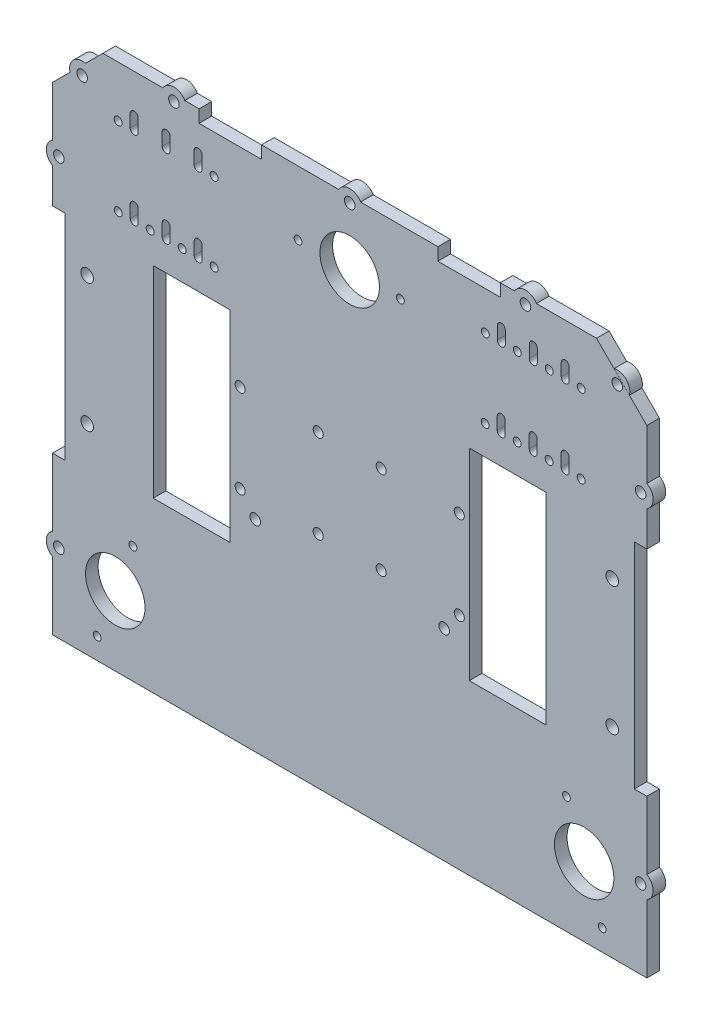
SolidWorks part; units mm, degrees
ref_plane "Front Plane" through (0, 0, 0) normal (0, 0, 1) x (1, 0, 0)
ref_plane "Top Plane" through (0, 0, 0) normal (0, 1, 0) x (1, 0, 0)
ref_plane "Right Plane" through (0, 0, 0) normal (1, 0, 0) x (0, 0, -1)
sketch "Sketch1" plane through (0, 0, 0) normal (0, 0, 1) x (1, 0, 0)
  line L0 (64.2262, -107) -> (118, -107)
  line L1 (-98, 103) -> (98, 103)
  line L3 (-118, -107) -> (-64.2262, -107)
  line L5 (-150, 100) -> (150, -100) construction
  line L6 (-150, -100) -> (150, 100) construction
  line L10 (0, 0) -> (0, 48.5738) construction
  line L12 (-47.5, 0) -> (47.5, 0) construction
  line L13 (47.5, -40) -> (47.5, 40)
  line L14 (47.5, 40) -> (78, 40)
  line L15 (78, 40) -> (78, -40)
  line L16 (78, -40) -> (47.5, -40)
  line L17 (-78, -40) -> (-47.5, -40)
  line L18 (-47.5, -40) -> (-47.5, 40)
  line L19 (-78, 40) -> (-78, -40)
  line L20 (-47.5, 40) -> (-78, 40)
  line L21 (78, 0) -> (118, 0) construction
  line L22 (118, 83) -> (118, -107)
  line L23 (-118, 83) -> (-118, -107)
  line L24 (-98, 103) -> (-98, 83) construction
  line L25 (-98, 83) -> (-118, 83) construction
  line L26 (0, 103) -> (0, -97) construction
  line L27 (-118, 83) -> (-98, 103)
  line L28 (98, 103) -> (118, 83)
  arc A0 (64.2262, -107) -> (-64.2262, -107) centre (0, -97) ccw
  point P0 (0, 0)
  point P19 (0, 0)
  point P22 (47.5, 0)
  point P33 (118, 0)
  dimension "D2" = 130
  dimension "D1" = 210
  dimension "D3" = 63
  dimension "D4" = 20
  dimension "D5" = 20
  dimension "D6" = 95
  dimension "D7" = 80
  dimension "D8" = 30.5
  dimension "D9" = 40
extrude "Boss-Extrude1" add sketch "Sketch1" along normal blind 5
sketch "Sketch2" plane through (0, 0, 5) normal (0, 0, 1) x (1, 0, 0)
  circle A0 centre (43.5, 15.5) radius 2
  circle A1 centre (43.5, -19.5) radius 2
  circle A2 centre (12.5, -19.5) radius 2
  circle A3 centre (12.5, 15.5) radius 2
  circle A4 centre (-12.5, 15.5) radius 2
  circle A5 centre (-12.5, -19.5) radius 2
  circle A6 centre (-43.5, -19.5) radius 2
  circle A7 centre (-43.5, 15.5) radius 2
extrude "Cut-Extrude1" cut sketch "Sketch2" against normal through all
sketch "Sketch3" plane through (0, 0, 5) normal (0, 0, 1) x (1, 0, 0)
  line L0 (-85.5875, 82.747) -> (-85.5875, 87.747) construction
  line L1 (-85.5875, 85.247) -> (-88.4029, 85.247) construction
  line L2 (-84, 87.747) -> (-84, 82.747)
  line L3 (-87.175, 87.747) -> (-87.175, 82.747)
  line L4 (-72.8875, 82.747) -> (-72.8875, 87.747) construction
  line L5 (-60.1875, 82.747) -> (-60.1875, 87.747) construction
  line L6 (-74.4775, 87.747) -> (-74.475, 82.747)
  line L7 (-71.2975, 87.747) -> (-71.3, 82.747)
  line L8 (-61.7775, 87.747) -> (-61.775, 82.747)
  line L9 (-58.5975, 87.747) -> (-58.6, 82.747)
  line L10 (-83.9734, 56.5828) -> (-83.9734, 51.5828)
  line L11 (-87.1484, 56.5828) -> (-87.1484, 51.5828)
  line L12 (-74.4509, 56.5828) -> (-74.4484, 51.5828)
  line L13 (-71.2709, 56.5828) -> (-71.2734, 51.5828)
  line L14 (-61.7509, 56.5828) -> (-61.7484, 51.5828)
  line L15 (-58.5709, 56.5828) -> (-58.5734, 51.5828)
  line L16 (0, 103) -> (0, 110.8506) construction
  line L17 (98, 103) -> (-98, 103) construction
  line L18 (60.1875, 82.747) -> (60.1875, 87.747) construction
  line L19 (72.8875, 82.747) -> (72.8875, 87.747) construction
  line L20 (85.5875, 85.247) -> (88.4029, 85.247) construction
  line L21 (85.5875, 82.747) -> (85.5875, 87.747) construction
  line L22 (58.5709, 56.5828) -> (58.5734, 51.5828)
  line L23 (61.7509, 56.5828) -> (61.7484, 51.5828)
  line L24 (71.2709, 56.5828) -> (71.2734, 51.5828)
  line L25 (74.4509, 56.5828) -> (74.4484, 51.5828)
  line L26 (87.1484, 56.5828) -> (87.1484, 51.5828)
  line L27 (83.9734, 56.5828) -> (83.9734, 51.5828)
  line L28 (58.5975, 87.747) -> (58.6, 82.747)
  line L29 (61.7775, 87.747) -> (61.775, 82.747)
  line L30 (71.2975, 87.747) -> (71.3, 82.747)
  line L31 (74.4775, 87.747) -> (74.475, 82.747)
  line L32 (87.175, 87.747) -> (87.175, 82.747)
  line L33 (84, 87.747) -> (84, 82.747)
  circle A0 centre (20.1383, 77.5) radius 1.55
  circle A1 centre (-20.5035, 77.5) radius 1.55
  circle A2 centre (-53.8375, 82.747) radius 1.5875
  circle A3 centre (-66.5375, 82.747) radius 1.5875
  circle A4 centre (-79.2375, 82.747) radius 1.5875
  circle A5 centre (-91.9375, 82.747) radius 1.5875
  circle A6 centre (0, 77.5) radius 11.8076
  circle A11 centre (-104.25, 23.5) radius 2.5
  circle A12 centre (-104.25, -27.5) radius 2.5
  circle A13 centre (104.25, 23.5) radius 2.5
  circle A14 centre (104.25, -27.5) radius 2.5
  circle A15 centre (86.0568, -60.5122) radius 1.55
  circle A16 centre (100.255, -98.5932) radius 1.55
  circle A17 centre (-86.0568, -60.5122) radius 1.55
  circle A18 centre (-100.255, -98.5932) radius 1.55
  arc A19 (-87.175, 82.747) -> (-84, 82.747) centre (-85.5875, 82.747) ccw
  arc A20 (-87.175, 87.747) -> (-84, 87.747) centre (-85.5875, 87.747) cw
  arc A21 (-74.475, 82.747) -> (-71.3, 82.747) centre (-72.8875, 82.747) ccw
  arc A22 (-61.775, 82.747) -> (-58.6, 82.747) centre (-60.1875, 82.747) ccw
  arc A23 (-71.2975, 87.747) -> (-74.4775, 87.747) centre (-72.8875, 87.747) ccw
  arc A24 (-58.5975, 87.747) -> (-61.7775, 87.747) centre (-60.1875, 87.747) ccw
  arc A25 (-61.775, 82.747) -> (-58.6, 82.747) centre (-60.1875, 82.747) ccw
  arc A27 (-87.1484, 56.5828) -> (-83.9734, 56.5828) centre (-85.5609, 56.5828) cw
  arc A28 (-87.1484, 51.5828) -> (-83.9734, 51.5828) centre (-85.5609, 51.5828) ccw
  arc A29 (-71.2709, 56.5828) -> (-74.4509, 56.5828) centre (-72.8609, 56.5828) ccw
  arc A30 (-74.4484, 51.5828) -> (-71.2734, 51.5828) centre (-72.8609, 51.5828) ccw
  arc A31 (-58.5709, 56.5828) -> (-61.7509, 56.5828) centre (-60.1609, 56.5828) ccw
  arc A32 (-61.7484, 51.5828) -> (-58.5734, 51.5828) centre (-60.1609, 51.5828) ccw
  circle A33 centre (-91.9109, 51.5828) radius 1.5875
  circle A34 centre (-79.2109, 51.5828) radius 1.5875
  circle A35 centre (-66.5109, 51.5828) radius 1.5875
  circle A36 centre (-53.8109, 51.5828) radius 1.5875
  circle A37 centre (53.8109, 51.5828) radius 1.5875
  circle A38 centre (66.5109, 51.5828) radius 1.5875
  circle A39 centre (79.2109, 51.5828) radius 1.5875
  circle A40 centre (91.9109, 51.5828) radius 1.5875
  arc A41 (61.7484, 51.5828) -> (58.5734, 51.5828) centre (60.1609, 51.5828) cw
  arc A42 (58.5709, 56.5828) -> (61.7509, 56.5828) centre (60.1609, 56.5828) cw
  arc A43 (74.4484, 51.5828) -> (71.2734, 51.5828) centre (72.8609, 51.5828) cw
  arc A44 (71.2709, 56.5828) -> (74.4509, 56.5828) centre (72.8609, 56.5828) cw
  arc A45 (87.1484, 51.5828) -> (83.9734, 51.5828) centre (85.5609, 51.5828) cw
  arc A46 (87.1484, 56.5828) -> (83.9734, 56.5828) centre (85.5609, 56.5828) ccw
  arc A47 (61.775, 82.747) -> (58.6, 82.747) centre (60.1875, 82.747) cw
  arc A48 (58.5975, 87.747) -> (61.7775, 87.747) centre (60.1875, 87.747) cw
  arc A49 (71.2975, 87.747) -> (74.4775, 87.747) centre (72.8875, 87.747) cw
  arc A50 (61.775, 82.747) -> (58.6, 82.747) centre (60.1875, 82.747) cw
  arc A51 (74.475, 82.747) -> (71.3, 82.747) centre (72.8875, 82.747) cw
  arc A52 (87.175, 87.747) -> (84, 87.747) centre (85.5875, 87.747) ccw
  arc A53 (87.175, 82.747) -> (84, 82.747) centre (85.5875, 82.747) cw
  circle A54 centre (91.9375, 82.747) radius 1.5875
  circle A55 centre (79.2375, 82.747) radius 1.5875
  circle A56 centre (66.5375, 82.747) radius 1.5875
  circle A57 centre (53.8375, 82.747) radius 1.5875
  circle A58 centre (93.0921, -79.3816) radius 11.8076
  circle A59 centre (-93.0921, -79.3816) radius 11.8076
  dimension "D4" = 3.18
  dimension "D1" = 5
  dimension "D3" = 5
  dimension "D5" = 2
  dimension "D6" = 2
extrude "Cut-Extrude2" cut sketch "Sketch3" against normal through all contours A6 | A0 | A1 | L7 A23 L6 A21 | L9 A24 L8 A22 | A20 L3 A19 L2 | A5 | A33 | L11 A28 L10 A27 | L12 A30 L13 A29 | A34 | L14 A32 L15 A31 | A35 | A36 | A53 L32 A52 L33 | A55 | A51 L31 A49 L30 | A48 L28 A47 L29 | A57 | A56 | A54 | L26 A46 L27 A45 | A40 | A39 | A44 L24 A43 L25 | A38 | A42 L22 A41 L23 | A37 | A13 | A14 | A58 | A15 | A16 | A11 | A12 | A59 | A18 | A17 | A2
sketch "Sketch4" plane through (0, 0, 5) normal (0, 0, 1) x (1, 0, 0)
  line L0 (-118, -2) -> (-113, -2) construction
  line L1 (-118, 83) -> (-118, -107) construction
  line L2 (-113, 40.5) -> (-113, -44.5)
  line L3 (-113, 40.5) -> (-118, 40.5)
  line L4 (-118, 40.5) -> (-118, -44.5)
  line L5 (-118, -44.5) -> (-113, -44.5)
  line L6 (0, 103) -> (0, 94.0884) construction
  line L7 (98, 103) -> (-98, 103) construction
  line L8 (118, -2) -> (113, -2) construction
  line L9 (118, -44.5) -> (113, -44.5)
  line L10 (118, 40.5) -> (118, -44.5)
  line L11 (113, 40.5) -> (118, 40.5)
  line L12 (113, 40.5) -> (113, -44.5)
  point P7 (-113, -2)
  point P20 (113, -2)
  dimension "D1" = 5
  dimension "D2" = 85
extrude "Cut-Extrude3" cut sketch "Sketch4" against normal through all
sketch "Sketch7" plane through (0, 0, 0) normal (0, 0, -1) x (-1, 0, 0)
  line L0 (-98, 103) -> (98, 103) construction
  line L1 (-59.8, 98) -> (-35, 98)
  line L2 (-59.8, 98) -> (-59.8, 103)
  line L3 (-59.8, 103) -> (-35, 103)
  line L4 (-35, 98) -> (-35, 103)
  line L5 (-59.8, 98) -> (-35, 103) construction
  line L6 (-59.8, 103) -> (-35, 98) construction
  line L7 (-35, 98) -> (-35, 103) construction
  line L8 (59.8, 98) -> (59.8, 103) construction
  line L9 (35, 98) -> (59.8, 98)
  line L10 (35, 98) -> (35, 103)
  line L11 (35, 103) -> (59.8, 103)
  line L12 (59.8, 98) -> (59.8, 103)
  line L13 (35, 98) -> (59.8, 103) construction
  line L14 (35, 103) -> (59.8, 98) construction
  line L15 (-35, 100.5) -> (35, 100.5) construction
  line L16 (59.8, 100.5) -> (69.8, 100.5) construction
  line L17 (-59.8, 100.5) -> (-69.8, 100.5) construction
  circle A0 centre (0, 100.5) radius 2.1
  circle A1 centre (69.8, 100.5) radius 2.1
  circle A2 centre (-69.8, 100.5) radius 2.1
  point P4 (-47.4, 100.5)
  point P14 (47.4, 100.5)
  dimension "D3" = 4.2
  dimension "D1" = 10
  dimension "D2" = 10
extrude "Cut-Extrude5" cut sketch "Sketch7" against normal through all
sketch "Sketch8" plane through (0, 0, 0) normal (0, 0, -1) x (-1, 0, 0)
  line L0 (-74.1301, 103) -> (-65.4699, 103)
  line L1 (-98, 103) -> (-59.8, 103) construction
  line L2 (-4.3301, 103) -> (4.3301, 103)
  line L3 (-35, 103) -> (35, 103) construction
  line L4 (65.4699, 103) -> (74.1301, 103)
  line L5 (59.8, 103) -> (98, 103) construction
  arc A0 (74.1301, 103) -> (65.4699, 103) centre (69.8, 100.5) ccw
  arc A1 (4.3301, 103) -> (-4.3301, 103) centre (0, 100.5) ccw
  arc A2 (-65.4699, 103) -> (-74.1301, 103) centre (-69.8, 100.5) ccw
  dimension "D1" = 10
extrude "Boss-Extrude3" add sketch "Sketch8" against normal up to surface (5 mm away) up to face at (0, 33.625, 5)
sketch "Sketch9" plane through (0, 0, 5) normal (0, 0, 1) x (1, 0, 0)
  circle A0 centre (37.5, -27) radius 2.1
  circle A1 centre (-37.5, -27) radius 2.1
extrude "Cut-Extrude6" cut sketch "Sketch9" against normal through all
sketch "Sketch10" plane through (0, 0, 0) normal (0, 0, -1) x (-1, 0, 0)
  line L0 (-118, -75.75) -> (-113, -75.75) construction
  line L1 (-118, -107) -> (-118, -44.5) construction
  line L2 (0, 0) -> (0, -17.3578) construction
  line L3 (113, 58.75) -> (118, 58.75) construction
  line L4 (113, 60.85) -> (113, 56.65) construction
  line L5 (118, 83) -> (118, 40.5) construction
  line L6 (-113, 58.75) -> (-118, 58.75) construction
  line L7 (-113, 56.65) -> (-113, 60.85) construction
  line L8 (-118, 40.5) -> (-118, 83) construction
  line L9 (-108, 93) -> (-104.466, 89.463) construction
  line L10 (-118, 83) -> (-98, 103) construction
  circle A0 centre (-115.5, -75.75) radius 2.1
  circle A1 centre (115.5, -75.75) radius 2.1
  circle A2 centre (-115.5, 58.75) radius 2.1
  circle A3 centre (115.5, 58.75) radius 2.1
  circle A4 centre (-106.233, 91.2315) radius 2.1
  circle A5 centre (106.233, 91.2315) radius 2.1
  point P36 (0, 0)
  point P37 (0, 0)
  point P38 (0, 0)
  point P39 (0, 0)
  point P40 (0, 0)
  dimension "D2" = 4.2
  dimension "D3" = 4.2
  dimension "D4" = 4.2
  dimension "D5" = 4.2
  dimension "D1" = 5
extrude "Cut-Extrude7" cut sketch "Sketch10" against normal blind 5
sketch "Sketch11" plane through (0, 0, 0) normal (0, 0, -1) x (-1, 0, 0)
  line L0 (-118, 54.4199) -> (-118, 63.0801)
  line L1 (-118, 40.5) -> (-118, 83) construction
  line L2 (-118, -71.4199) -> (-118, -80.0801)
  line L3 (-118, -107) -> (-118, -44.5) construction
  line L4 (118, -71.4199) -> (118, -80.0801)
  line L5 (118, -44.5) -> (118, -107) construction
  line L6 (118, 63.0801) -> (118, 54.4199)
  line L7 (118, 83) -> (118, 40.5) construction
  line L8 (104.9389, 96.0611) -> (111.0626, 89.9374)
  line L9 (98, 103) -> (118, 83) construction
  line L10 (-104.9992, 96.0769) -> (-111.0626, 89.9374)
  line L11 (-118, 83) -> (-98, 103) construction
  arc A0 (-118, 63.0801) -> (-118, 54.4199) centre (-115.5, 58.75) ccw
  arc A1 (-118, -71.4199) -> (-118, -80.0801) centre (-115.5, -75.75) ccw
  arc A2 (118, -80.0801) -> (118, -71.4199) centre (115.5, -75.75) ccw
  arc A3 (118, 54.4199) -> (118, 63.0801) centre (115.5, 58.75) ccw
  arc A4 (-104.9992, 96.0769) -> (-111.0626, 89.9374) centre (-106.233, 91.2315) ccw
  arc A5 (111.0626, 89.9374) -> (104.9389, 96.0611) centre (106.233, 91.2315) ccw
  dimension "D1" = 10
extrude "Boss-Extrude4" add sketch "Sketch11" against normal blind 5
sketch "Sketch12" plane through (0, 0, 0) normal (0, 0, -1) x (-1, 0, 0)
  line L0 (-91.1131, -107) -> (-91.1131, -114) construction
  line L1 (-64.2262, -107) -> (-118, -107) construction
  line L2 (-91.1131, -114) -> (-131.1131, -114) construction
  line L3 (-118, -107) -> (-131.1131, -114)
  line L5 (-91.1131, -114) -> (-91.1131, -184) construction
  line L6 (-131.1131, -114) -> (-130.96, -132.6461)
  line L8 (-118, -107) -> (-64.2262, -107)
  line L9 (0, -107) -> (0, -144.2151) construction
  line L10 (118, -107) -> (-118, -107) construction
  line L11 (91.1131, -114) -> (131.1131, -114) construction
  line L12 (91.1131, -107) -> (91.1131, -114) construction
  line L13 (118, -107) -> (64.2262, -107)
  line L15 (131.1131, -114) -> (130.96, -132.6461)
  line L17 (118, -107) -> (131.1131, -114)
  line L18 (-64.2262, -107) -> (-64.2262, -124.8215)
  line L19 (64.2262, -107) -> (64.2262, -124.8215)
  arc A1 (-64.2262, -124.8215) -> (-130.96, -132.6461) centre (-91.1131, -184) ccw
  arc A2 (64.2262, -124.8215) -> (130.96, -132.6461) centre (91.1131, -184) cw
  dimension "D4" = 130
  dimension "D1" = 7
  dimension "D2" = 40
  dimension "D3" = 70
extrude "Boss-Extrude5" add sketch "Sketch12" against normal blind 5
sketch "Esquisse1" plane through (0, 0, 5) normal (0, 0, 1) x (1, 0, 0)
  line L1 (-153.1521, -107) -> (157.1692, -107)
  line L2 (-153.1521, -107) -> (-153.1521, -145.1928)
  line L3 (-153.1521, -145.1928) -> (157.1692, -145.1928)
  line L4 (157.1692, -107) -> (157.1692, -145.1928)
extrude "Enlèv. mat.-Extru.1" cut sketch "Esquisse1" against normal blind 10
sketch "Esquisse2" plane through (0, 0, 5) normal (0, 0, 1) x (1, 0, 0)
  line L0 (-64.2262, -107) -> (64.2262, -107)
  arc A0 (64.2262, -107) -> (-64.2262, -107) centre (0, -97) ccw construction
  arc A1 (64.2262, -107) -> (-64.2262, -107) centre (0, -97) ccw
extrude "Boss.-Extru.1" add sketch "Esquisse2" against normal blind 5
